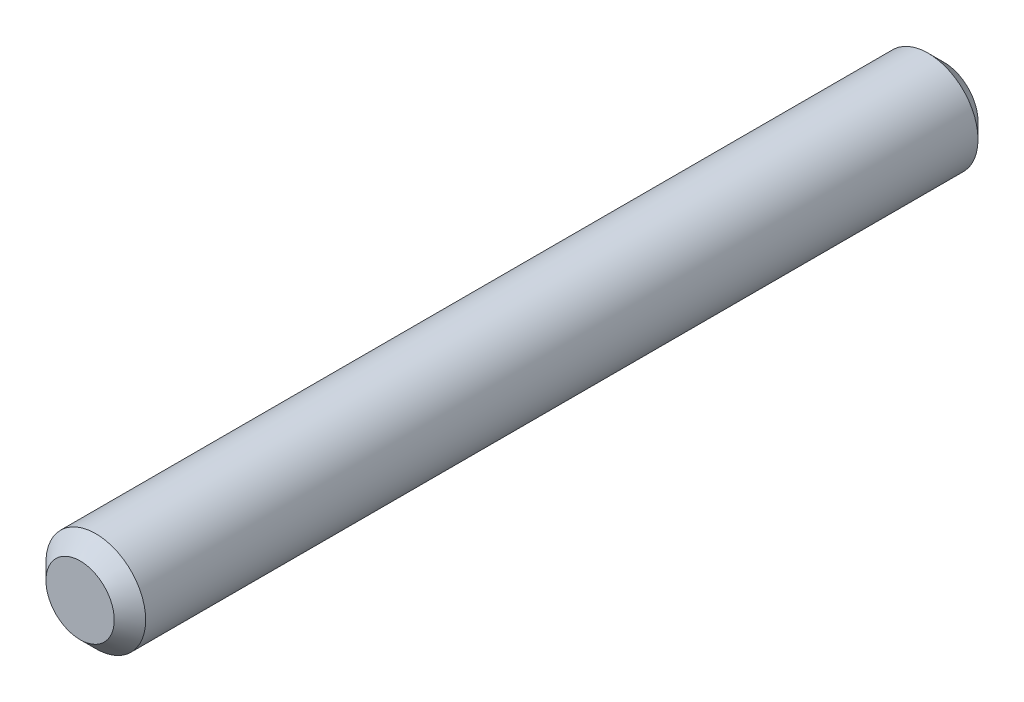
SolidWorks part; units mm, degrees
material "AISI 1020"
ref_plane "Front Plane" through (0, 0, 0) normal (0, 0, 1) x (1, 0, 0)
ref_plane "Top Plane" through (0, 0, 0) normal (0, 1, 0) x (1, 0, 0)
ref_plane "Right Plane" through (0, 0, 0) normal (1, 0, 0) x (0, 0, -1)
sketch "Sketch1" plane through (0, 0, 0) normal (0, 0, 1) x (1, 0, 0)
  circle A0 centre (0, 0) radius 3.175
  dimension "D1" = 6.35
extrude "Boss-Extrude1" add sketch "Sketch1" against normal blind 55
cosmetic thread "Cosmetic Thread1" parameters "D2"=5.268
chamfer "Chamfer1" distance 1 angle 45 2 edges at (3.175, 0, -55) (3.175, 0, 0)
